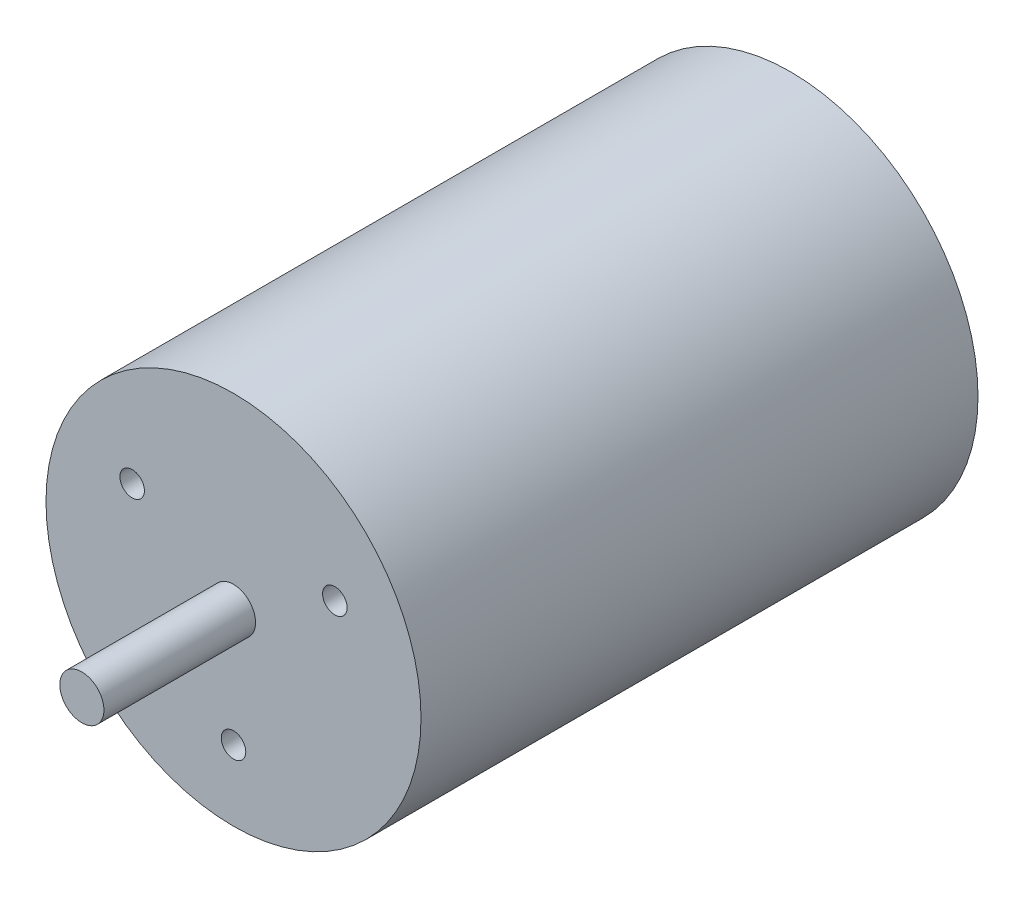
SolidWorks part; units mm, degrees
ref_plane "Front Plane" through (0, 0, 0) normal (0, 0, 1) x (1, 0, 0)
ref_plane "Top Plane" through (0, 0, 0) normal (0, 1, 0) x (1, 0, 0)
ref_plane "Right Plane" through (0, 0, 0) normal (1, 0, 0) x (0, 0, -1)
sketch "Sketch1" plane through (0, 0, 0) normal (0, 0, 1) x (1, 0, 0)
  circle A0 centre (0, 0) radius 34
  dimension "D1" = 68
extrude "Boss-Extrude1" add sketch "Sketch1" along normal blind 101
sketch "Sketch2" plane through (0, 0, 101) normal (0, 0, 1) x (1, 0, 0)
  circle A0 centre (0, 0) radius 4
  dimension "D1" = 8
extrude "Boss-Extrude2" add sketch "Sketch2" along normal blind 27.5
sketch "Sketch3" plane through (0, 0, 101) normal (0, 0, 1) x (1, 0, 0)
  line L0 (0, 0) -> (-18.375, 10.6088) construction
  line L1 (-18.375, 10.6088) -> (18.375, 10.6088) construction
  line L2 (18.375, 10.6088) -> (0, -21.2176) construction
  circle A0 centre (0, 0) radius 21.2176 construction
  circle A1 centre (-18.375, 10.6088) radius 2.225
  circle A2 centre (18.375, 10.6088) radius 2.225
  circle A3 centre (0, -21.2176) radius 2.225
  dimension "D1" = 4.45
  dimension "D2" = 41.2
extrude "Cut-Extrude1" cut sketch "Sketch3" against normal blind 20
sketch "Sketch4" plane through (0, 0, 0) normal (0, 0, -1) x (-1, 0, 0)
  circle A0 centre (0, 0) radius 14
  dimension "D1" = 28
extrude "Boss-Extrude3" add sketch "Sketch4" along normal blind 7
